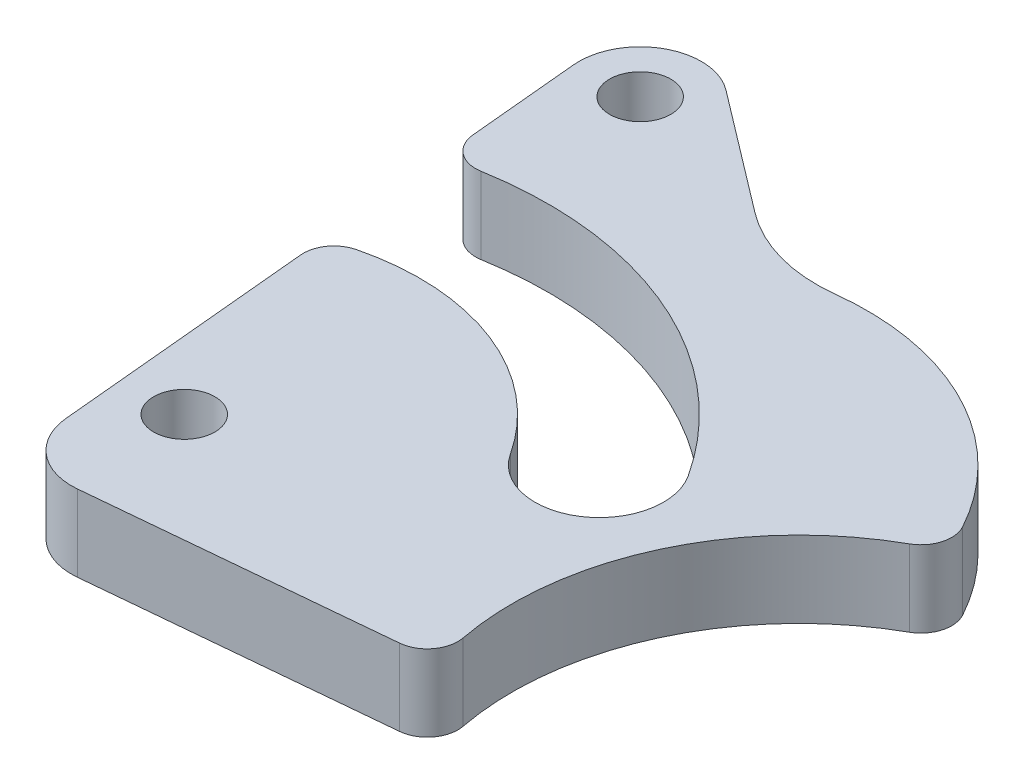
SolidWorks part; units mm, degrees
ref_plane "前视基准面" through (0, 0, 0) normal (0, 0, 1) x (1, 0, 0)
ref_plane "上视基准面" through (0, 0, 0) normal (0, 1, 0) x (1, 0, 0)
ref_plane "右视基准面" through (0, 0, 0) normal (1, 0, 0) x (0, 0, -1)
sketch "草图1" plane through (0, 0, 0) normal (0, 1, 0) x (1, 0, 0)
  line L0 (-20.0875, 0) -> (20.0875, 0) construction
  line L1 (-20.0875, 0) -> (-23.165, 32.8682) construction
  line L2 (-20.0875, 0) -> (-23.165, 32.8682) construction
  line L3 (-23.165, 32.8682) -> (20.0875, 0) construction
  line L4 (-20.0875, 0) -> (-23.165, 32.8682) construction
  line L5 (-24.0701, -0.3729) -> (-27.1475, 32.4954)
  line L6 (-16.1049, 0.3729) -> (-19.1824, 33.2411)
  line L7 (-23.165, 32.8682) -> (20.0875, 0) construction
  line L8 (-20.7448, 36.053) -> (22.5077, 3.1848)
  line L9 (-25.5851, 29.6835) -> (17.6673, -3.1848)
  line L10 (-20.0875, 0) -> (20.0875, 0) construction
  line L11 (-20.0875, 4) -> (20.0875, 4)
  line L12 (-20.0875, -4) -> (20.0875, -4)
  arc A0 (-24.0701, -0.3729) -> (-16.1049, 0.3729) centre (-20.0875, 0) ccw
  arc A1 (-19.1824, 33.2411) -> (-27.1475, 32.4954) centre (-23.165, 32.8682) ccw
  arc A2 (-20.7448, 36.053) -> (-25.5851, 29.6835) centre (-23.165, 32.8682) ccw
  arc A3 (17.6673, -3.1848) -> (22.5077, 3.1848) centre (20.0875, 0) ccw
  arc A4 (-20.0875, 4) -> (-20.0875, -4) centre (-20.0875, 0) ccw
  arc A5 (20.0875, -4) -> (20.0875, 4) centre (20.0875, 0) ccw
  circle A6 centre (-20.0875, 0) radius 2
  circle A7 centre (-23.165, 32.8682) radius 2
  circle A8 centre (20.0875, 0) radius 2
  point P4 (0, 0)
  point P7 (-21.6262, 16.4341)
  point P12 (-1.5387, 16.4341)
  point P18 (0, 0)
  dimension "D4" = 4
  dimension "D5" = 4
  dimension "D6" = 4
  dimension "D7" = 4
  dimension "D1" = 40.175
  dimension "D2" = 33.012
  dimension "D3" = 54.324
extrude "凸台-拉伸1" add sketch "草图1" along normal blind 5 contours L11 A4 A0 L6 A6 | A4 L11 L6 L9 A2 L5 | A1 A2 L9 L6 A7 | A5 L8 A1 L6 L9 L11 | A3 L9 L11 L6 A0 L12 | A3 A5 L11 L9 A8 | L6 L11 L9
sketch "草图2" plane through (0, 5, 0) normal (0, 1, 0) x (1, 0, 0)
  line L0 (-23.165, 32.8682) -> (-20.0875, 0) construction
  line L1 (-20.0875, 0) -> (-19.7384, -3.7287) construction
  line L2 (-19.7384, -3.7287) -> (20.0875, 0) construction
  line L3 (-20.1113, 0.2539) -> (19.7146, 3.9826)
  line L4 (-19.3655, -7.7113) -> (20.4604, -3.9826)
  line L5 (-23.721, -4.1016) -> (-24.3127, 2.2182)
  line L6 (-24.0701, -0.3729) -> (-27.1475, 32.4954) construction
  arc A0 (-20.1113, 0.2539) -> (-19.3655, -7.7113) centre (-19.7384, -3.7287) ccw
  arc A1 (20.4604, -3.9826) -> (19.7146, 3.9826) centre (20.0875, 0) ccw
  point P4 (0.1746, -1.8643)
  dimension "D2" = 4
  dimension "D1" = 3.745
extrude "凸台-拉伸2" add sketch "草图2" against normal blind 5
sketch "草图3" plane through (0, 5, 0) normal (0, 1, 0) x (1, 0, 0)
  circle A0 centre (-20.0875, 0) radius 19.6
  arc A1 (-33.4302, 14.3573) -> (-3.6558, 10.6846) centre (-20.0875, 0) cw construction
  arc A2 (-0.1348, 12.9742) -> (-36.2893, 17.4339) centre (-20.0875, 0) ccw
  arc A3 (-7.1769, 8.395) -> (-30.571, 11.2808) centre (-20.0875, 0) ccw
  arc A4 (-7.1769, 8.395) -> (-0.1348, 12.9742) centre (-3.6558, 10.6846) ccw
  arc A5 (-36.2893, 17.4339) -> (-30.571, 11.2808) centre (-33.4302, 14.3573) ccw
  point P5 (-17.688, 19.4526)
  line M3 (-27.1475, 32.4954) -> (-23.721, -4.1016)
  dimension "D1" = 39.2
  dimension "D2" = 4.2
  dimension "D3" = 30
extrude "切除-拉伸1" cut sketch "草图3" against normal through all contours A2 A5 A0 M3 | A0 A4 A2 M3 | A3 A4 A0 M3 | A0 A5 A3 M3
sketch "草图4" plane through (0, 5, 0) normal (0, 1, 0) x (1, 0, 0)
  circle A0 centre (-3.6558, 10.6846) radius 17.5
  line M11 (22.5077, 3.1848) -> (-20.7448, 36.053)
  dimension "D1" = 35
extrude "凸台-拉伸3" add sketch "草图4" against normal blind 5 contours A0 M11
fillet "圆角1" radius 10 2 edges at (13.8211, 2.5, -9.7859) (-9.2029, 2.5, -27.2822)
fillet "圆角2" radius 2 2 edges at (-25.4564, 2.5, -14.4338) (-26.2572, 2.5, -22.9864)
sketch "草图6" plane through (0, 5, 0) normal (0, 1, 0) x (1, 0, 0)
  circle A0 centre (20.0875, 0) radius 18.75
  dimension "D1" = 37.5
extrude "切除-拉伸2" cut sketch "草图6" against normal through all
fillet "圆角3" radius 2 2 edges at (12.5915, 2.5, -17.1864) (2.2218, 2.5, 5.6902)
sketch "草图7" [suppressed] plane through (0, 5, 0) normal (0, 1, 0) x (1, 0, 0)
  line L0 (-19.3655, -7.7113) -> (-13.3916, -7.152)
  line L1 (-19.3655, -7.7113) -> (-1.3531, -6.0249) construction
  line L2 (-13.3916, -7.152) -> (-12.9256, -12.1302)
  line L3 (-12.9256, -12.1302) -> (-18.8994, -12.6895)
  line L4 (-18.8994, -12.6895) -> (-19.3655, -7.7113)
  dimension "D1" = 5
  dimension "D2" = 6
